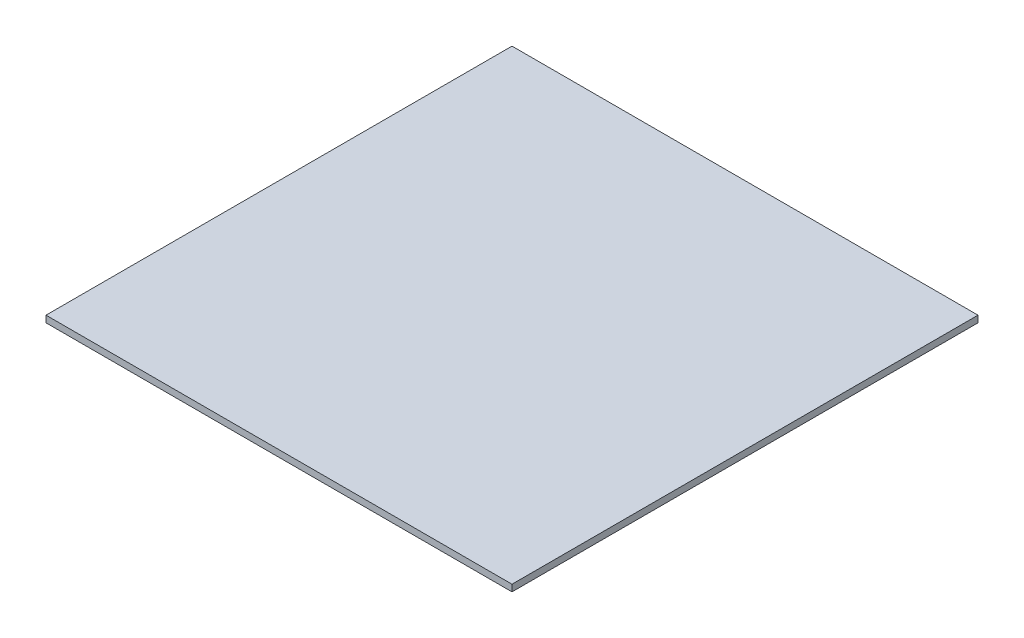
SolidWorks part; units mm, degrees
material "MDF"
ref_plane "Front Plane" through (0, 0, 0) normal (0, 0, 1) x (1, 0, 0)
ref_plane "Top Plane" through (0, 0, 0) normal (0, 1, 0) x (1, 0, 0)
ref_plane "Right Plane" through (0, 0, 0) normal (1, 0, 0) x (0, 0, -1)
sketch "Sketch1" plane through (0, 0, 0) normal (0, 1, 0) x (1, 0, 0)
  line L1 (0, 0) -> (889, 0)
  line L2 (0, 0) -> (0, 889)
  line L3 (0, 889) -> (889, 889)
  line L4 (889, 0) -> (889, 889)
  dimension "D1" = 889
  dimension "D2" = 889
extrude "Boss-Extrude1" add sketch "Sketch1" along normal blind 12.7
